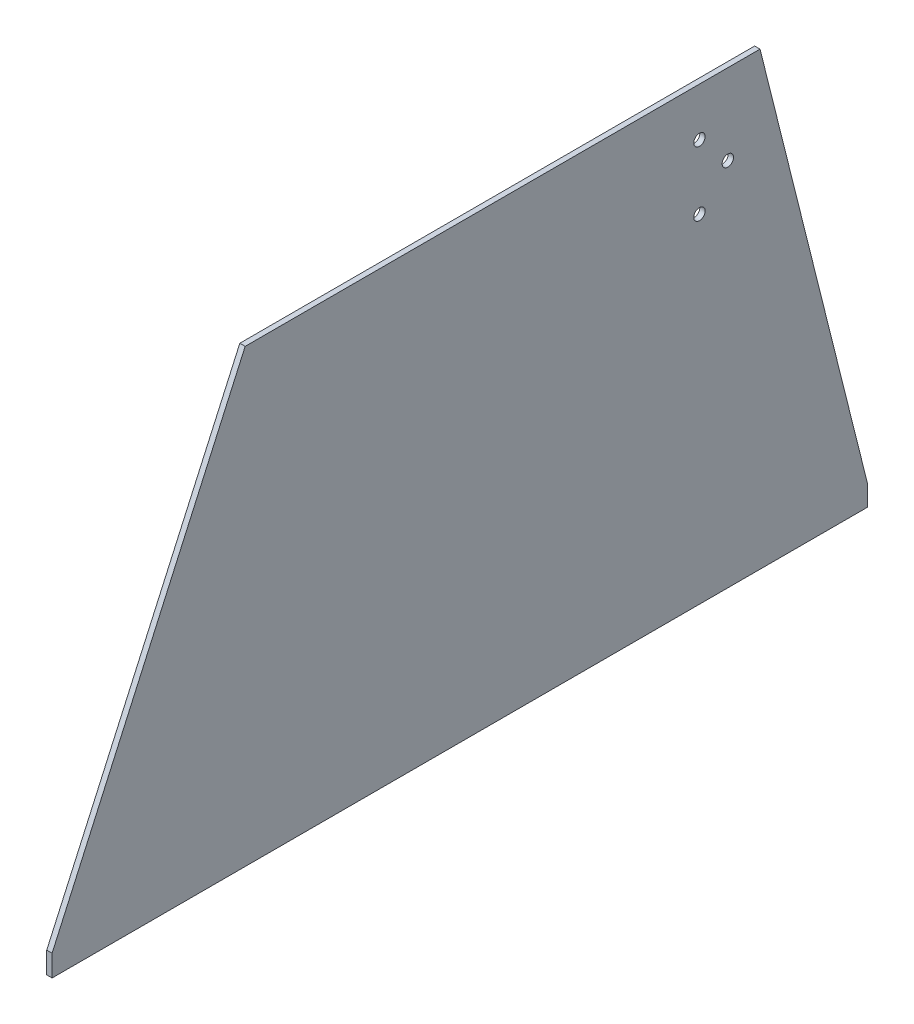
SolidWorks part; units mm, degrees
material "6061-T6 (SS)"
ref_plane "Front Plane" through (0, 0, 0) normal (0, 0, 1) x (1, 0, 0)
ref_plane "Top Plane" through (0, 0, 0) normal (0, 1, 0) x (1, 0, 0)
ref_plane "Right Plane" through (0, 0, 0) normal (1, 0, 0) x (0, 0, -1)
sketch "Sketch1" plane through (0, 0, 0) normal (1, 0, 0) x (0, 0, -1)
  line L1 (114.3, 266.7) -> (419.1, 266.7)
  line L2 (419.1, 266.7) -> (482.6, 12.7)
  line L3 (482.6, 12.7) -> (482.6, 0)
  line L4 (482.6, 0) -> (0, 0)
  line L5 (0, 12.7) -> (0, 0)
  line L6 (114.3, 266.7) -> (0, 12.7)
  point P0 (526.3252, 330.2)
  point P9 (-158.8473, 330.2)
  dimension "D1" = 114.3
  dimension "D2" = 266.7
  dimension "D3" = 482.6
  dimension "D4" = 12.7
  dimension "D5" = 12.7
  dimension "D6" = 63.5
extrude "Boss-Extrude1" add sketch "Sketch1" along normal blind 3.175
sketch "Sketch2" [suppressed] plane through (3.175, 0, 0) normal (1, 0, 0) x (0, 0, -1)
  line L0 (-279.4, 0) -> (279.4, 0) construction
  line L1 (254, 0) -> (228.6, 0)
  line L2 (254, 0) -> (254, 19.05)
  line L3 (247.65, 25.4) -> (234.95, 25.4)
  line L4 (228.6, 0) -> (228.6, 19.05)
  line L6 (203.2, 0) -> (177.8, 0)
  line L7 (203.2, 0) -> (203.2, 19.05)
  line L8 (196.85, 25.4) -> (184.15, 25.4)
  line L9 (177.8, 0) -> (177.8, 19.05)
  line L10 (152.4, 0) -> (127, 0)
  line L11 (152.4, 0) -> (152.4, 19.05)
  line L12 (146.05, 25.4) -> (133.35, 25.4)
  line L13 (127, 0) -> (127, 19.05)
  line L14 (101.6, 0) -> (76.2, 0)
  line L15 (101.6, 0) -> (101.6, 19.05)
  line L16 (95.25, 25.4) -> (82.55, 25.4)
  line L17 (76.2, 0) -> (76.2, 19.05)
  line L18 (50.8, 0) -> (25.4, 0)
  line L19 (50.8, 0) -> (50.8, 19.05)
  line L20 (44.45, 25.4) -> (31.75, 25.4)
  line L21 (25.4, 0) -> (25.4, 19.05)
  line L22 (50.8, 0) -> (76.2, 0) construction
  line L23 (101.6, 0) -> (127, 0) construction
  line L24 (152.4, 0) -> (177.8, 0) construction
  line L25 (203.2, 0) -> (228.6, 0) construction
  line L27 (279.4, 0) -> (279.4, 12.7) construction
  line L28 (0, 609.6) -> (0, 0) construction
  arc A0 (31.75, 25.4) -> (25.4, 19.05) centre (31.75, 19.05) ccw
  arc A1 (50.8, 19.05) -> (44.45, 25.4) centre (44.45, 19.05) ccw
  arc A2 (82.55, 25.4) -> (76.2, 19.05) centre (82.55, 19.05) ccw
  arc A3 (101.6, 19.05) -> (95.25, 25.4) centre (95.25, 19.05) ccw
  arc A4 (133.35, 25.4) -> (127, 19.05) centre (133.35, 19.05) ccw
  arc A5 (152.4, 19.05) -> (146.05, 25.4) centre (146.05, 19.05) ccw
  arc A6 (184.15, 25.4) -> (177.8, 19.05) centre (184.15, 19.05) ccw
  arc A7 (203.2, 19.05) -> (196.85, 25.4) centre (196.85, 19.05) ccw
  arc A8 (234.95, 25.4) -> (228.6, 19.05) centre (234.95, 19.05) ccw
  arc A9 (254, 19.05) -> (247.65, 25.4) centre (247.65, 19.05) ccw
  point P52 (254, 25.4)
  dimension "D5" = 6.35
  dimension "D1" = 25.4
  dimension "D2" = 25.4
  dimension "D3" = 25.4
  dimension "D4" = 25.4
extrude "Cut-Extrude1" [suppressed] cut sketch "Sketch2" against normal through all
sketch "Sketch3" plane through (3.175, 0, 0) normal (1, 0, 0) x (0, 0, -1)
  line L0 (0, 0) -> (482.6, 0) construction
  line L3 (482.6, 0) -> (482.6, 12.7) construction
  circle A0 centre (400.05, 219.075) radius 3.3782
  circle A1 centre (383.2495, 200.025) radius 3.3782
  circle A2 centre (383.2495, 238.125) radius 3.3782
  point P8 (0, 0)
  dimension "D1" = 6.7564
  dimension "D2" = 219.075
  dimension "D3" = 82.55
  dimension "D4" = 25.4
  dimension "D5" = 25.4
  dimension "D6" = 38.1
extrude "Cut-Extrude2" cut sketch "Sketch3" against normal through all
